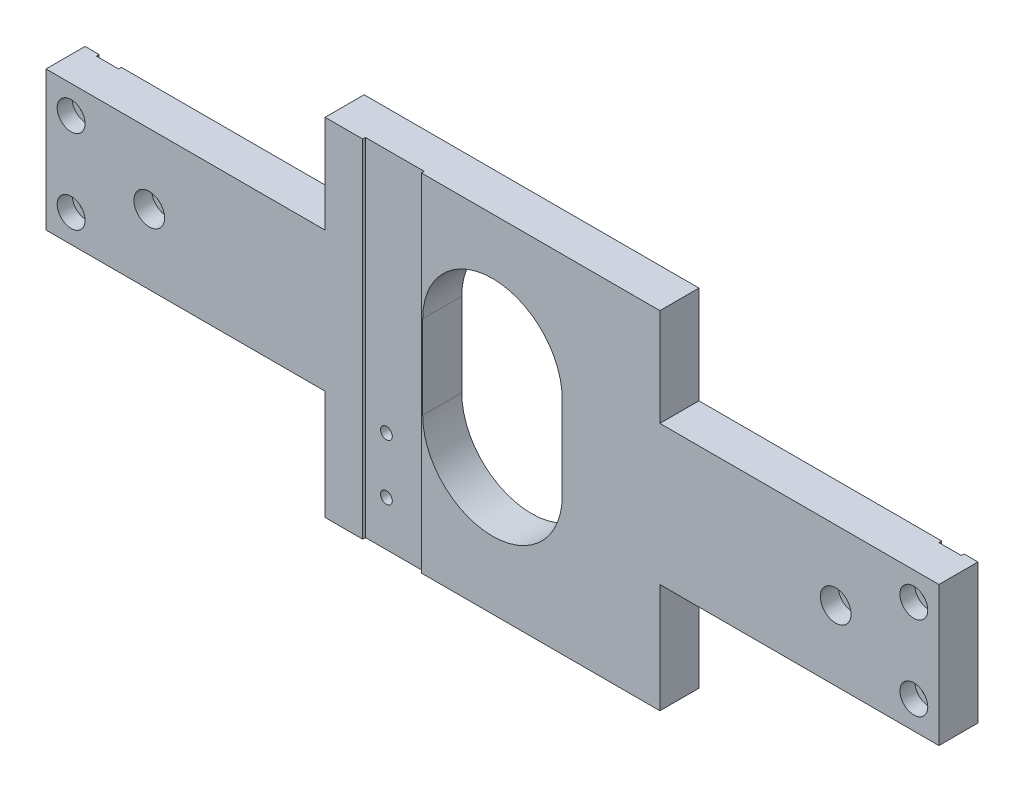
SolidWorks part; units mm, degrees
ref_plane "前视基准面" through (0, 0, 0) normal (0, 0, 1) x (1, 0, 0)
ref_plane "上视基准面" through (0, 0, 0) normal (0, 1, 0) x (1, 0, 0)
ref_plane "右视基准面" through (0, 0, 0) normal (1, 0, 0) x (0, 0, -1)
sketch "草图1" plane through (0, 0, 0) normal (0, 0, 1) x (1, 0, 0)
  line L1 (0, 0) -> (320, 0)
  line L2 (0, 0) -> (0, 50)
  line L3 (0, 50) -> (320, 50)
  line L4 (320, 0) -> (320, 50)
  dimension "D1" = 320
  dimension "D2" = 50
extrude "凸台-拉伸1" add sketch "草图1" along normal blind 14
hole_wizard "M6 六角凹头螺钉的柱形沉头孔1" positions "草图3" profile "草图4" counterbore size "M6" standard "ISO" end condition through all
sketch "草图3" plane through (0, 0, 14) normal (0, 0, 1) x (1, 0, 0)
  line L0 (160, 0) -> (160, 50) construction
  line L1 (0, 0) -> (320, 0) construction
  line L2 (320, 50) -> (0, 50) construction
  line L5 (160, 25) -> (114.5936, 25) construction
  point P0 (283, 25)
  point P2 (37, 25)
  dimension "D1" = 246
sketch "草图4" plane through (283, 25, 14) normal (1, 0, 0) x (0, -1, 0)
  line L0 (0, 0) -> (0, 14)
  line L1 (0, 14) -> (3.3, 14)
  line L3 (3.3, 14) -> (3.3, 6.4)
  line L4 (3.3, 6.4) -> (5.5, 6.4)
  line L5 (5.5, 6.4) -> (5.5, 0)
  line L7 (5.5, 0) -> (0, 0)
  line L11 (0, -6.35) -> (0, 107.95) construction
  dimension "通孔孔直径" = 6.6
  dimension "通孔孔深度" = 14
  dimension "柱形沉头孔直径" = 11
  dimension "柱形沉头孔深度" = 6.4
sketch "草图5" plane through (0, 0, 0) normal (0, 0, -1) x (-1, 0, 0)
  circle A0 centre (-283, 25) radius 6
  circle A1 centre (-37, 25) radius 6
  dimension "D1" = 12
  dimension "D2" = 12
extrude "切除-拉伸1" cut sketch "草图5" against normal blind 3
sketch "草图6" plane through (0, 0, 0) normal (0, 0, -1) x (-1, 0, 0)
  line L0 (-320, 50) -> (0, 50) construction
  line L1 (-13, 50) -> (-5, 50)
  line L2 (-13, 50) -> (-13, 0)
  line L3 (-13, 0) -> (-5, 0)
  line L4 (-5, 50) -> (-5, 0)
  line L5 (0, 0) -> (-320, 0) construction
  line L6 (0, 50) -> (0, 0) construction
  line L7 (-160, 50) -> (-160, 0) construction
  line L8 (-307, 0) -> (-315, 0)
  line L9 (-307, 50) -> (-307, 0)
  line L10 (-307, 50) -> (-315, 50)
  line L11 (-315, 50) -> (-315, 0)
  dimension "D1" = 8
  dimension "D2" = 5
extrude "切除-拉伸2" cut sketch "草图6" against normal blind 1
hole_wizard "M5 六角凹头螺钉的柱形沉头孔1" positions "草图7" profile "草图8" counterbore size "M5" standard "ISO" end condition through all
sketch "草图7" plane through (0, 0, 14) normal (0, 0, 1) x (1, 0, 0)
  line L0 (320, 25) -> (242.5477, 25) construction
  line L1 (320, 0) -> (320, 50) construction
  line L3 (160, 0) -> (160, 50) construction
  line L4 (0, 0) -> (320, 0) construction
  line L5 (320, 50) -> (0, 50) construction
  point P0 (311, 10)
  point P2 (311, 40)
  point P18 (9, 40)
  point P19 (9, 10)
  dimension "D1" = 30
  dimension "D2" = 9
sketch "草图8" plane through (311, 10, 14) normal (1, 0, 0) x (0, -1, 0)
  line L0 (0, 0) -> (0, 14)
  line L1 (0, 14) -> (2.75, 14)
  line L3 (2.75, 14) -> (2.75, 5.4)
  line L4 (2.75, 5.4) -> (5, 5.4)
  line L5 (5, 5.4) -> (5, 0)
  line L7 (5, 0) -> (0, 0)
  line L11 (0, -6.35) -> (0, 107.95) construction
  dimension "通孔孔直径" = 5.5
  dimension "通孔孔深度" = 14
  dimension "柱形沉头孔直径" = 10
  dimension "柱形沉头孔深度" = 5.4
sketch "草图9" plane through (0, 0, 0) normal (0, -1, 0) x (1, 0, 0)
  line L0 (160, 14) -> (160, -22.2682) construction
  line L1 (0, 14) -> (320, 14) construction
  line L2 (13, 0) -> (307, 0) construction
  line L3 (145, 14) -> (175, 14)
  line L4 (145, 14) -> (145, 0)
  line L5 (145, 0) -> (175, 0)
  line L6 (175, 14) -> (175, 0)
  dimension "D1" = 30
extrude "切除-拉伸3" cut sketch "草图9" against normal blind 15
sketch "草图10" plane through (0, 0, 14) normal (0, 0, 1) x (1, 0, 0)
  line L0 (320, 25) -> (0, 25) construction
  line L1 (320, 0) -> (320, 50) construction
  line L2 (0, 50) -> (0, 0) construction
  line L3 (0, 25) -> (160, 25) construction
  line L4 (160, 25) -> (160, -59.287) construction
  line L6 (220, -25) -> (100, -25)
  line L7 (220, -25) -> (220, 75)
  line L8 (220, 75) -> (100, 75)
  line L9 (100, -25) -> (100, 75)
  circle A0 centre (160, 25) radius 39
  dimension "D3" = 78
  dimension "D1" = 120
  dimension "D2" = 100
extrude "凸台-拉伸2" add sketch "草图10" against normal up to surface (14 mm away) up to face at (160, 16.25, 0)
sketch "草图15" plane through (0, 0, 14) normal (0, 0, 1) x (1, 0, 0)
  circle A0 centre (160, 25) radius 39
extrude "凸台-拉伸3" add sketch "草图15" against normal up to surface (14 mm away) up to face at (160, 25, 0)
sketch "草图16" plane through (0, 0, 14) normal (0, 0, 1) x (1, 0, 0)
  line L0 (160, -25) -> (160, 75) construction
  line L1 (100, -25) -> (220, -25) construction
  line L2 (220, 75) -> (100, 75) construction
  line L3 (160, 75) -> (160, 25) construction
  line L4 (160, 25) -> (94.6207, 25) construction
  line L7 (185, 10) -> (185, 40)
  line L9 (135, 10) -> (135, 40)
  arc A1 (135, 40) -> (185, 40) centre (160, 40) cw
  arc A2 (135, 10) -> (185, 10) centre (160, 10) ccw
extrude "切除-拉伸4" cut sketch "草图16" against normal blind 31.5
sketch "草图17" plane through (0, -25, 0) normal (0, -1, 0) x (1, 0, 0)
  line L1 (100, 14) -> (220, 14)
  line L2 (100, 14) -> (100, 0)
  line L3 (100, 0) -> (220, 0)
  line L4 (220, 14) -> (220, 0)
extrude "凸台-拉伸4" add sketch "草图17" along normal blind 14.2
sketch "草图18" plane through (0, 75, 0) normal (0, 1, 0) x (1, 0, 0)
  line L1 (220, -14) -> (100, -14)
  line L2 (220, -14) -> (220, 0)
  line L3 (220, 0) -> (100, 0)
  line L4 (100, -14) -> (100, 0)
extrude "凸台-拉伸5" add sketch "草图18" along normal blind 10
hole_wizard "M5 螺纹孔1" positions "草图19" profile "草图20" tap size "M5" standard "ISO"
sketch "草图19" plane through (0, 0, 14) normal (0, 0, 1) x (1, 0, 0)
  line L0 (220, -39.2) -> (100, -39.2) construction
  point P0 (121, -3)
  point P2 (121, -23)
  dimension "D1" = 20
  dimension "D2" = 16.2
sketch "草图20" plane through (121, -3, 14) normal (1, 0, 0) x (0, -1, 0)
  line L0 (0, 0) -> (0, 13.6618)
  line L1 (0, 13.6618) -> (2.1, 12.4)
  line L2 (2.1, 12.4) -> (2.1, 0)
  line L5 (2.1, 0) -> (0, 0)
  line L10 (0, 13.6618) -> (-2.1, 12.4) construction
  line L11 (0, -6.35) -> (0, 107.95) construction
  dimension "螺纹孔钻头直径" = 4.2
  dimension "螺纹孔钻头深度" = 12.4
  dimension "导头角度" = 118
cosmetic thread "孔螺蚊线1" parameters "D1"=10, "D2"=5
cosmetic thread "孔螺蚊线2" parameters "D1"=10, "D2"=5
sketch "草图21" plane through (0, 0, 14) normal (0, 0, 1) x (1, 0, 0)
  line L0 (220, -39.2) -> (100, -39.2) construction
  line L1 (134.5, -39.2) -> (113.5, -39.2)
  line L2 (134.5, -39.2) -> (134.5, 85)
  line L3 (134.5, 85) -> (113.5, 85)
  line L4 (113.5, -39.2) -> (113.5, 85)
  line L5 (134.5, 18.2) -> (134.5, -38.2) construction
  line L6 (100, 85) -> (220, 85) construction
extrude "切除-拉伸5" cut sketch "草图21" against normal blind 1
hole_wizard "M5 螺纹孔2" positions "草图23" profile "草图24" tap size "M5" standard "ISO"
sketch "草图23" plane through (0, -39.2, 0) normal (0, -1, 0) x (-1, 0, 0)
  line L0 (-100, -7) -> (-220, -7) construction
  line L1 (-100, -14) -> (-100, 0) construction
  line L2 (-220, 0) -> (-220, -14) construction
  line L3 (-220, -7) -> (-160, -7) construction
  line L4 (-160, -7) -> (-160, -38.6969) construction
  point P18 (-160, -7)
  point P25 (-110, -7)
  point P31 (-210, -7)
  dimension "D1" = 100
sketch "草图24" plane through (160, -39.2, 7) normal (1, 0, 0) x (0, 0, -1)
  line L0 (0, 0) -> (0, 13.6618)
  line L1 (0, 13.6618) -> (2.1, 12.4)
  line L2 (2.1, 12.4) -> (2.1, 0)
  line L5 (2.1, 0) -> (0, 0)
  line L10 (0, 13.6618) -> (-2.1, 12.4) construction
  line L11 (0, -6.35) -> (0, 107.95) construction
  dimension "螺纹孔钻头直径" = 4.2
  dimension "螺纹孔钻头深度" = 12.4
  dimension "导头角度" = 118
cosmetic thread "孔螺蚊线3" parameters "D1"=10, "D2"=5
cosmetic thread "孔螺蚊线4" parameters "D1"=10, "D2"=5
cosmetic thread "孔螺蚊线5" parameters "D1"=10, "D2"=5
